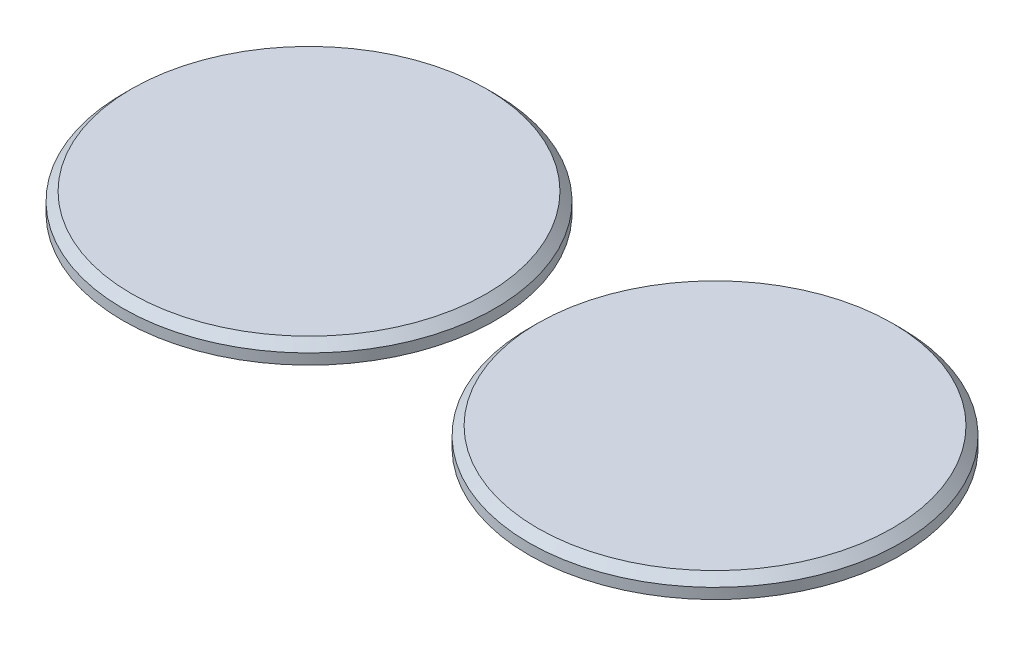
SolidWorks part; units mm, degrees
ref_plane "Front Plane" through (0, 0, 0) normal (0, 0, 1) x (1, 0, 0)
ref_plane "Top Plane" through (0, 0, 0) normal (0, 1, 0) x (1, 0, 0)
ref_plane "Right Plane" through (0, 0, 0) normal (1, 0, 0) x (0, 0, -1)
sketch "Sketch1" plane through (0, 0, 0) normal (0, 1, 0) x (1, 0, 0)
  line L1 (0, 0) -> (152.4, 0)
  line L2 (0, 0) -> (0, 84.074)
  line L3 (0, 84.074) -> (152.4, 84.074)
  line L4 (152.4, 0) -> (152.4, 84.074)
  dimension "D1" = 152.4
  dimension "D2" = 84.074
extrude "stock" add sketch "Sketch1" along normal blind 3.302
sketch "Sketch2" plane through (0, 3.302, 0) normal (0, 1, 0) x (1, 0, 0)
  line L0 (0, 84.074) -> (0, 0) construction
  line L1 (0, 0) -> (152.4, 0) construction
  circle A0 centre (32.3, 32.3) radius 27.3
  circle A1 centre (91.9, 32.3) radius 27.3
  point P4 (0, 0)
  line M3 (0, 84.074) -> (0, 0)
  line M4 (0, 0) -> (152.4, 0)
  line M5 (152.4, 0) -> (152.4, 84.074)
  line M6 (152.4, 84.074) -> (0, 84.074)
  dimension "D1" = 54.6
  dimension "D2" = 54.6
  dimension "D3" = 5
  dimension "D4" = 5
  dimension "D5" = 5
extrude "disks-clearout" cut sketch "Sketch2" against normal through all both and the other way through all contours A1 A0 M6 M3 M4 M5
chamfer "disk0-cham0" distance 1.75 angle 45 1 edges at (32.3, 3.302, -59.6)
chamfer "disk1-cham1" distance 1.75 angle 45 1 edges at (91.9, 3.302, -59.6)
ref_plane "Plane1" through (0, 3.302, 0) normal (0, 1, 0) x (1, 0, 0)
sketch "Sketch3" plane through (0, 3.302, 0) normal (0, 1, 0) x (1, 0, 0)
  circle A0 centre (32.3, 32.3) radius 27.3
  circle A1 centre (91.9, 32.3) radius 27.3
  circle A2 centre (91.9, 32.3) radius 27.3 construction
  circle A3 centre (32.3, 32.3) radius 27.3 construction
extrude "topsurface_surfaceprep" cut sketch "Sketch3" against normal blind 0.5 and the other way through all
